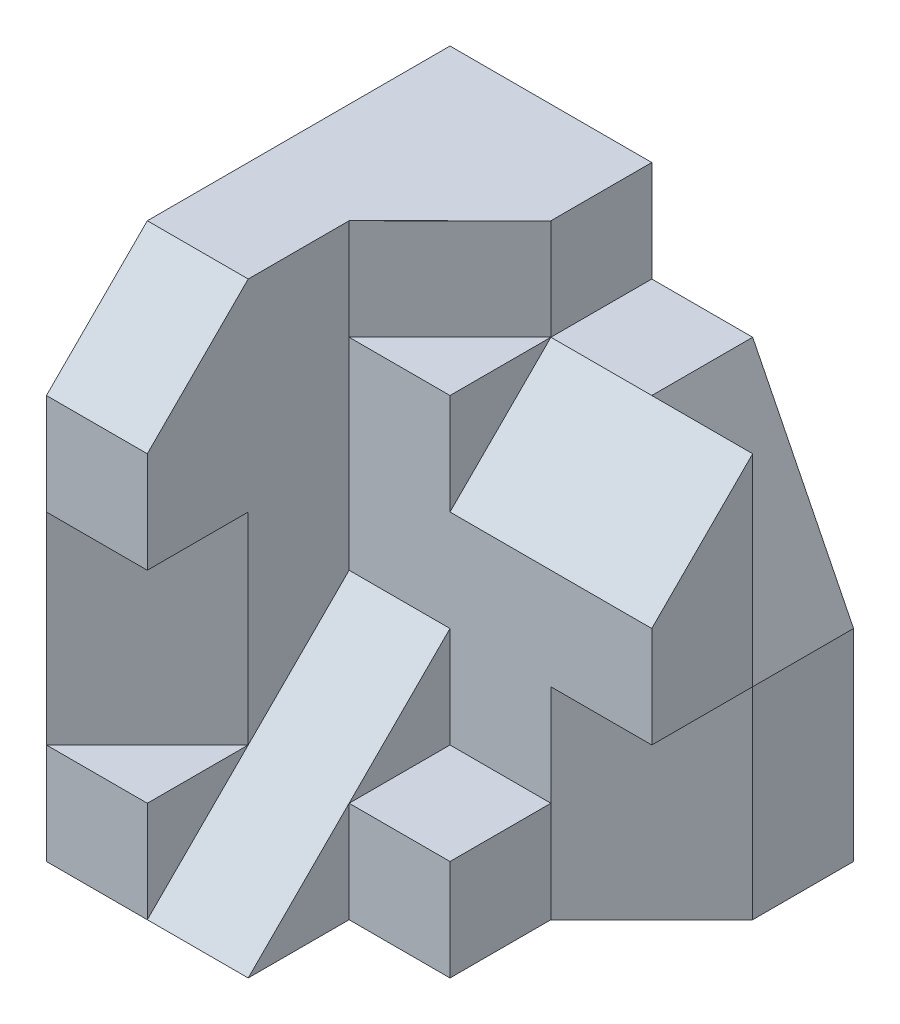
SolidWorks part; units mm, degrees
ref_plane "Front Plane" through (0, 0, 0) normal (0, 0, 1) x (1, 0, 0)
ref_plane "Top Plane" through (0, 0, 0) normal (0, 1, 0) x (1, 0, 0)
ref_plane "Right Plane" through (0, 0, 0) normal (1, 0, 0) x (0, 0, -1)
sketch "Sketch1" plane through (0, 0, 0) normal (0, 0, 1) x (1, 0, 0)
  line L1 (2, -2.5) -> (-2, -2.5)
  line L2 (2, -2.5) -> (2, 2.5)
  line L3 (2, 2.5) -> (-2, 2.5)
  line L4 (-2, -2.5) -> (-2, 2.5)
  line L5 (2, -2.5) -> (-2, 2.5) construction
  line L6 (2, 2.5) -> (-2, -2.5) construction
  point P0 (0, 0)
  dimension "D1" = 5
  dimension "D2" = 4
extrude "Boss-Extrude1" add sketch "Sketch1" along normal blind 4
sketch "Sketch2" plane through (2, 0, 0) normal (1, 0, 0) x (0, 0, -1)
  line L0 (-3, 2.5) -> (-4, 1.5)
  line L1 (-4, 2.5) -> (0, 2.5) construction
  line L2 (-4, -2.5) -> (-4, 2.5) construction
  line L3 (-4, 1.5) -> (-4, 2.5)
  line L4 (-4, 2.5) -> (-3, 2.5)
  dimension "D1" = 1
  dimension "D2" = 1
extrude "Cut-Extrude1" cut sketch "Sketch2" against normal through all
sketch "Sketch3" plane through (0, 2.5, 0) normal (0, 1, 0) x (1, 0, 0)
  line L0 (2, 0) -> (0, 0)
  line L1 (2, 0) -> (-2, 0) construction
  line L2 (0, 0) -> (0, -1)
  line L3 (0, -1) -> (-1, -2)
  line L4 (-1, -2) -> (-1, -3)
  line L5 (-2, -3) -> (2, -3) construction
  line L6 (-1, -3) -> (2, -3)
  line L7 (2, -3) -> (2, 0)
  dimension "D1" = 1
  dimension "D2" = 1
  dimension "D3" = 1
  dimension "D4" = 2
extrude "Cut-Extrude2" cut sketch "Sketch3" against normal blind 1
sketch "Sketch4" plane through (0, 0, 0) normal (0, 0, -1) x (-1, 0, 0)
  line L0 (-2, 1.5) -> (-1, 1.5)
  line L1 (-2, 1.5) -> (0, 1.5) construction
  line L2 (-1, 1.5) -> (-2, -0.5)
  line L3 (-2, -2.5) -> (-2, 1.5) construction
  line L4 (-2, -0.5) -> (-2, 1.5)
  dimension "D1" = 2
extrude "Cut-Extrude3" cut sketch "Sketch4" against normal blind 1
sketch "Sketch5" plane through (2, 0, 0) normal (1, 0, 0) x (0, 0, -1)
  line L0 (-1, 1.5) -> (-2, 0.5)
  line L1 (-2, 0.5) -> (-2, 1.5)
  line L2 (-2, 1.5) -> (-1, 1.5)
  dimension "D1" = 1
extrude "Cut-Extrude4" cut sketch "Sketch5" against normal blind 2
sketch "Sketch6" plane through (0, 2.5, 0) normal (0, 1, 0) x (1, 0, 0)
  line L0 (2, -4) -> (2, -2)
  line L1 (2, -3) -> (2, -2) construction
  line L2 (0, -2) -> (2, -2) construction
  line L3 (2, -2) -> (0, -2)
  line L4 (0, -2) -> (0, -4)
  line L5 (-2, -4) -> (2, -4) construction
  line L6 (0, -4) -> (2, -4)
  dimension "D1" = 2
extrude "Cut-Extrude5" cut sketch "Sketch6" against normal blind 4
sketch "Sketch7" plane through (0, -1.5, 0) normal (0, 1, 0) x (1, 0, 0)
  line L0 (2, -2) -> (1, -2)
  line L1 (1, -2) -> (1, -3)
  line L2 (1, -3) -> (0, -3)
  line L3 (0, -3) -> (0, -4)
  line L4 (-2, -4) -> (0, -4) construction
  line L5 (0, -4) -> (0, -3) construction
  line L6 (0, -4) -> (2, -4)
  line L7 (2, -4) -> (2, -2)
  dimension "D1" = 1
extrude "Cut-Extrude6" cut sketch "Sketch7" against normal through all
sketch "Sketch8" plane through (0, 0, 0) normal (1, 0, 0) x (0, 0, -1)
  line L0 (-2, -0.5) -> (-4, -2.5)
  line L1 (-2, -1.5) -> (-2, 0.5) construction
  line L2 (-4, -2.5) -> (-4, 2.5)
  line L3 (-4, 2.5) -> (-2, 2.5)
  line L4 (-2, 2.5) -> (-2, -0.5)
  dimension "D1" = 5
extrude "Cut-Extrude7" cut sketch "Sketch8" against normal blind 1
sketch "Sketch9" plane through (0, -2.5, 0) normal (0, -1, 0) x (1, 0, 0)
  line L0 (1, 2) -> (2, 1)
  line L1 (2, 2) -> (2, 0) construction
  line L2 (2, 1) -> (2, 2)
  line L3 (2, 2) -> (1, 2)
extrude "Cut-Extrude8" cut sketch "Sketch9" against normal blind 2
sketch "Sketch10" plane through (0, 0.75, 0.75) normal (0, 0.7071, 0.7071) x (1, 0, 0)
  line L0 (-1, -4.5962) -> (-1, -1.7678) construction
  point P0 (-1, -3.182)
sketch "Sketch11" plane through (0, 0, 4) normal (0, 0, 1) x (1, 0, 0)
  line L0 (-2, 1.5) -> (-2, -2.5) construction
  point P0 (-2, -1.5)
  dimension "D1" = 1
ref_plane "Plane1" through (1, 0, 1) normal (-0.7071, 0, -0.7071) x (-0.7071, 0, 0.7071)
sketch "Sketch12" plane through (1, 0, 1) normal (-0.7071, 0, -0.7071) x (-0.7071, 0, 0.7071)
  line L0 (2.8284, -1.5) -> (4.2426, -1.5)
  line L1 (4.2426, -1.5) -> (4.2426, 0.5)
  line L2 (4.2426, 1.5) -> (4.2426, -2.5) construction
  line L3 (4.2426, 0.5) -> (2.8284, 0.5)
  line L4 (2.8284, 0.5) -> (2.8284, -1.5)
  dimension "D1" = 2
extrude "Cut-Extrude9" cut sketch "Sketch12" against normal through all
